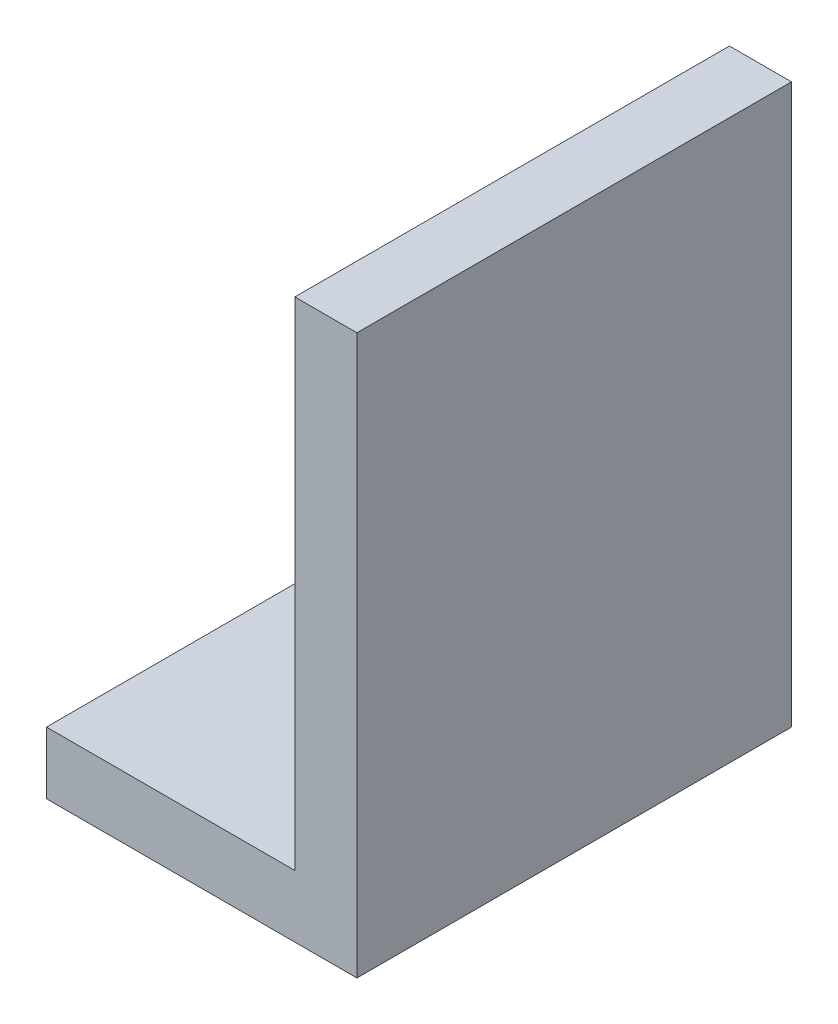
SolidWorks part; units mm, degrees
ref_plane "Front Plane" through (0, 0, 0) normal (0, 0, 1) x (1, 0, 0)
ref_plane "Top Plane" through (0, 0, 0) normal (0, 1, 0) x (1, 0, 0)
ref_plane "Right Plane" through (0, 0, 0) normal (1, 0, 0) x (0, 0, -1)
sketch "Sketch1" plane through (0, 0, 0) normal (0, 0, 1) x (1, 0, 0)
  line L0 (0, 0) -> (50, 0)
  line L1 (50, 0) -> (50, 90)
  line L2 (50, 90) -> (40, 90)
  line L3 (40, 90) -> (40, 10)
  line L4 (0, 0) -> (0, 10)
  line L5 (0, 10) -> (40, 10)
  dimension "D1" = 10
  dimension "D2" = 10
  dimension "D3" = 40
  dimension "D4" = 80
extrude "Boss-Extrude1" add sketch "Sketch1" along normal blind 70
